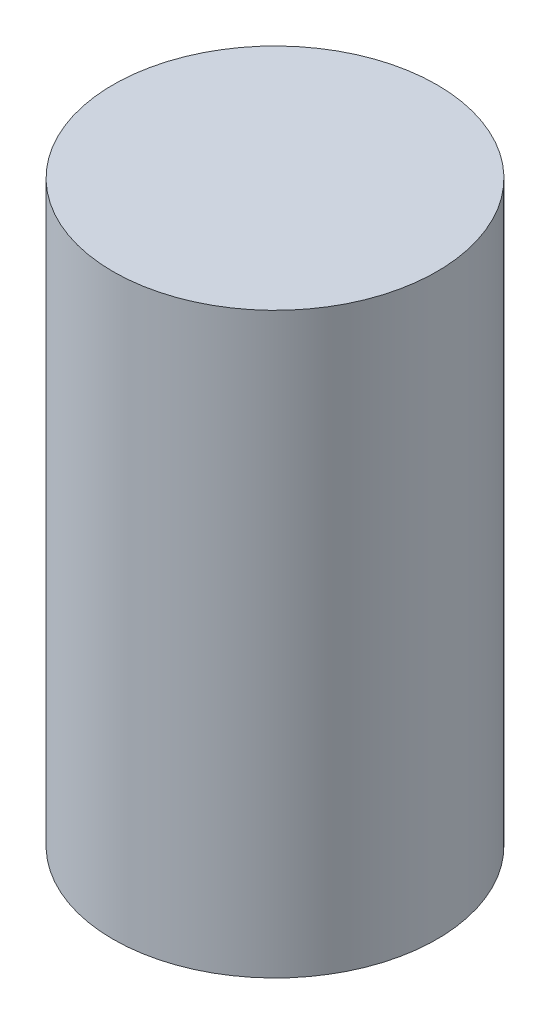
SolidWorks part; units mm, degrees
ref_plane "Front Plane" through (0, 0, 0) normal (0, 0, 1) x (1, 0, 0)
ref_plane "Top Plane" through (0, 0, 0) normal (0, 1, 0) x (1, 0, 0)
ref_plane "Right Plane" through (0, 0, 0) normal (1, 0, 0) x (0, 0, -1)
sketch "Sketch1" plane through (0, 0, 0) normal (0, 1, 0) x (1, 0, 0)
  circle A0 centre (0, 0) radius 7
  dimension "D1" = 14
extrude "Boss-Extrude1" add sketch "Sketch1" along normal blind 25
